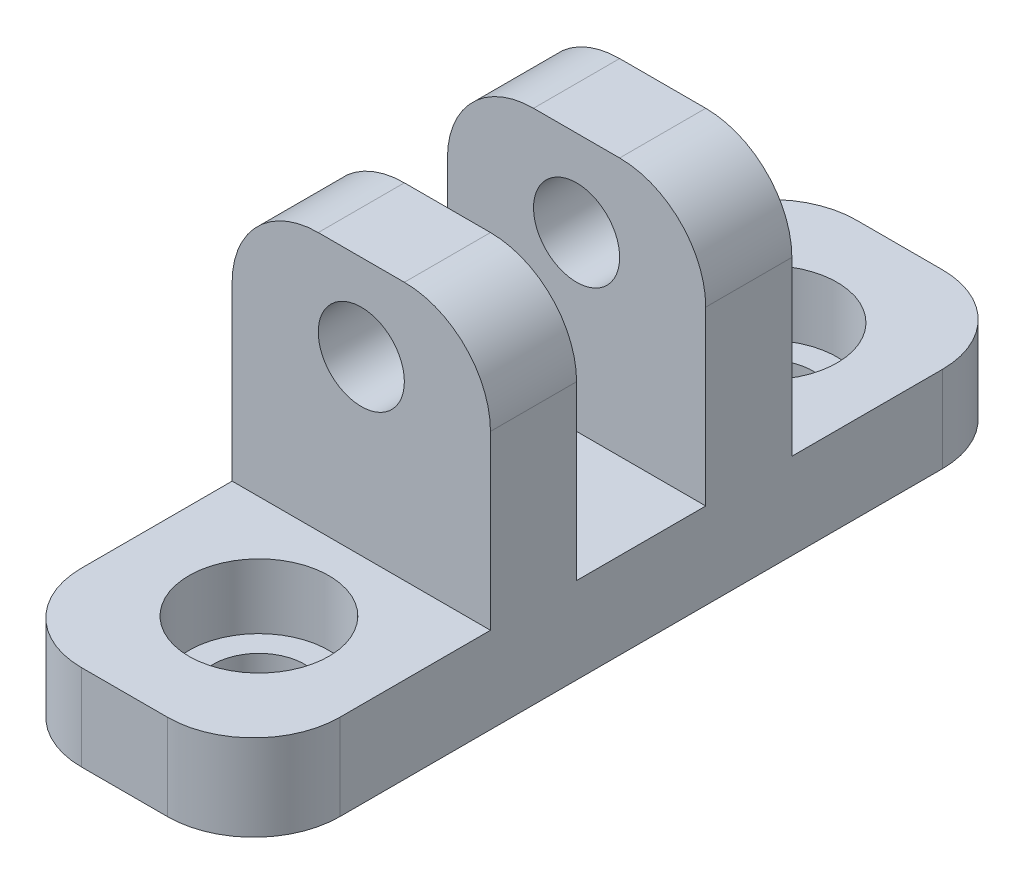
SolidWorks part; units mm, degrees
material "6061-T6 (SS)"
ref_plane "Front Plane" through (0, 0, 0) normal (0, 0, 1) x (1, 0, 0)
ref_plane "Top Plane" through (0, 0, 0) normal (0, 1, 0) x (1, 0, 0)
ref_plane "Right Plane" through (0, 0, 0) normal (1, 0, 0) x (0, 0, -1)
sketch "Sketch1" plane through (0, 0, 0) normal (0, 1, 0) x (1, 0, 0)
  line L0 (60.325, 0) -> (0, 0) construction
  line L1 (60.325, 28.575) -> (79.375, 28.575)
  line L2 (60.325, 28.575) -> (60.325, -28.575)
  line L3 (60.325, -28.575) -> (79.375, -28.575)
  line L4 (79.375, 28.575) -> (79.375, -28.575)
  circle A0 centre (0, 0) radius 72.39 construction
  dimension "D1" = 144.78
  dimension "D2" = 19.05
  dimension "D3" = 57.15
  dimension "D4" = 60.325
extrude "Boss-Extrude1" add sketch "Sketch1" along normal blind 25.4
sketch "Sketch2" plane through (79.375, 0, 0) normal (1, 0, 0) x (0, 0, -1)
  line L0 (-28.575, 25.4) -> (28.575, 25.4) construction
  line L1 (-28.575, 25.4) -> (-11.1125, 25.4)
  line L2 (-28.575, 25.4) -> (-28.575, 6.35)
  line L3 (-28.575, 6.35) -> (-11.1125, 6.35)
  line L4 (-11.1125, 25.4) -> (-11.1125, 6.35)
  line L5 (-4.7625, 25.4) -> (4.7625, 25.4)
  line L6 (-4.7625, 25.4) -> (-4.7625, 6.35)
  line L7 (-4.7625, 6.35) -> (4.7625, 6.35)
  line L8 (4.7625, 25.4) -> (4.7625, 6.35)
  line L10 (28.575, 25.4) -> (11.1125, 25.4)
  line L11 (28.575, 25.4) -> (28.575, 6.35)
  line L12 (28.575, 6.35) -> (11.1125, 6.35)
  line L13 (11.1125, 25.4) -> (11.1125, 6.35)
  line L14 (-28.575, 0) -> (28.575, 0) construction
  line L16 (0, 25.4) -> (0, 6.35) construction
  dimension "D1" = 6.35
  dimension "D2" = 9.525
  dimension "D3" = 6.35
extrude "Cut-Extrude1" cut sketch "Sketch2" against normal through all
ref_plane "Plane1" through (0, 0, 0) normal (0, 0, 1) x (1, 0, 0)
sketch "Sketch9" plane through (0, 0, 11.1125) normal (0, 0, 1) x (1, 0, 0)
  line L0 (60.325, 25.4) -> (79.375, 25.4) construction
  line L2 (69.85, 19.05) -> (69.85, 25.4) construction
  circle A0 centre (69.85, 19.05) radius 3.175
  dimension "D1" = 6.35
  dimension "D2" = 6.35
extrude "Cut-Extrude3" cut sketch "Sketch9" against normal through all
fillet "Fillet1" radius 6.35 8 edges at (60.325, 3.175, -28.575) (79.375, 3.175, -28.575) (60.325, 3.175, 28.575) (79.375, 3.175, 28.575) (79.375, 25.4, -7.9375) (60.325, 25.4, -7.9375) (60.325, 25.4, 7.9375) (79.375, 25.4, 7.9375)
hole_wizard "CBORE for 1/4 Socket Shoulder Screw1" positions "Sketch10" profile "Sketch11" counterbore size "1/4" standard "ANSI Inch" end condition through all
sketch "Sketch10" plane through (0, 6.35, 0) normal (0, 1, 0) x (1, 0, 0)
  line L0 (0, 0) -> (72.39, 0) construction
  line L2 (0, 0) -> (69.9234, 18.7359)
  line L4 (0, 0) -> (69.9234, -18.7359)
  line L6 (72.39, 0) -> (79.375, 0)
  line L7 (79.375, -4.7625) -> (79.375, 4.7625) construction
  circle A0 centre (0, 0) radius 72.39
  point P10 (69.9234, 18.7359)
  point P15 (69.9234, -18.7359)
  dimension "D1" = 144.78
  dimension "D2" = 30
  dimension "D3" = 15
sketch "Sketch11" plane through (69.9234, 6.35, -18.7359) normal (1, 0, 0) x (0, 0, 1)
  line L0 (0, 0) -> (0, 6.35)
  line L1 (0, 6.35) -> (3.3782, 6.35)
  line L3 (3.3782, 6.35) -> (3.3782, 4.7752)
  line L4 (3.3782, 4.7752) -> (5.1587, 4.7752)
  line L5 (5.1587, 4.7752) -> (5.1587, 0)
  line L7 (5.1587, 0) -> (0, 0)
  line L11 (0, -6.35) -> (0, 107.95) construction
  dimension "Thru Hole Dia." = 6.7564
  dimension "Thru Hole Depth" = 6.35
  dimension "C'Bore Dia." = 10.3175
  dimension "C'Bore Depth" = 4.7752
equation "\"D3@Sketch10\"=\"D2@Sketch10\"/2"
